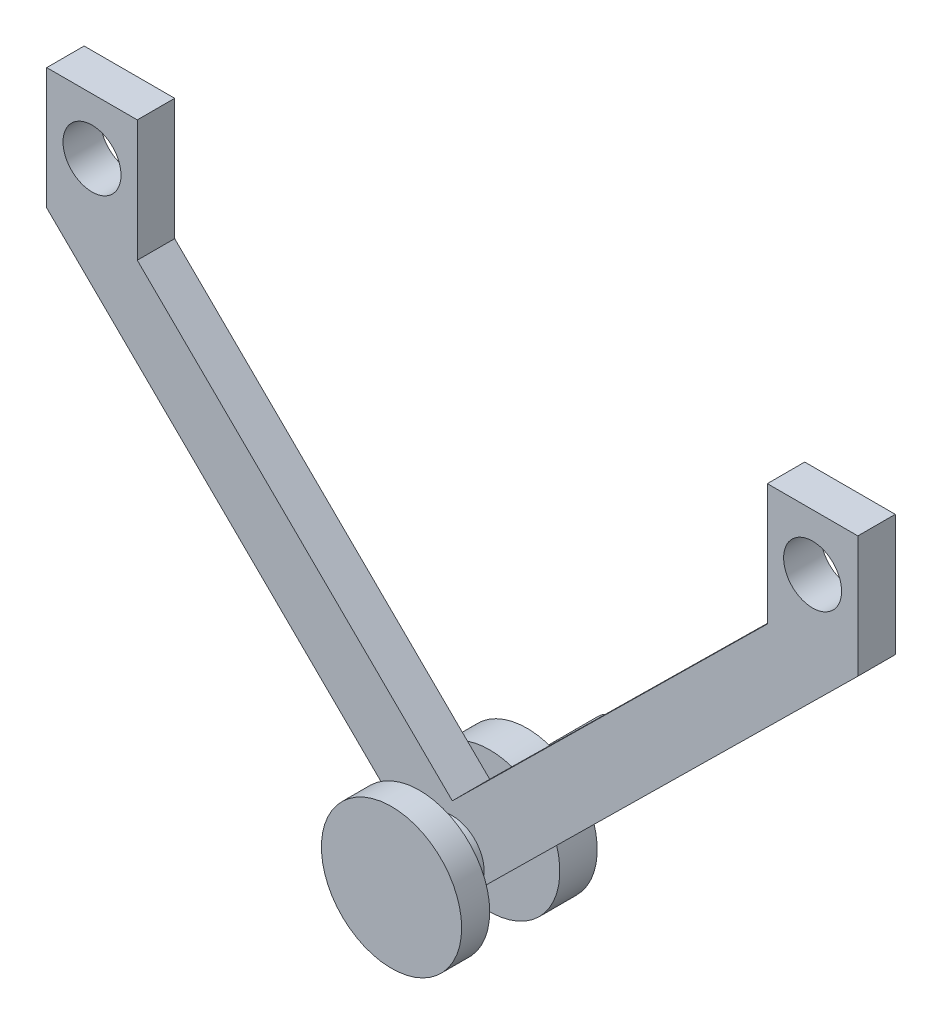
SolidWorks part; units mm, degrees
ref_plane "Спереди" through (0, 0, 0) normal (0, 0, 1) x (1, 0, 0)
ref_plane "Сверху" through (0, 0, 0) normal (0, 1, 0) x (1, 0, 0)
ref_plane "Справа" through (0, 0, 0) normal (1, 0, 0) x (0, 0, -1)
sketch "Эскиз1" plane through (0, 0, 0) normal (0, 0, 1) x (1, 0, 0)
  circle A0 centre (0, 0) radius 7.5
  point P2 (0, 0)
  dimension "D1" = 15
extrude "Бобышка-Вытянуть1" add sketch "Эскиз1" against normal blind 3
sketch "Эскиз2" plane through (0, 0, -3) normal (0, 0, -1) x (-1, 0, 0)
  circle A0 centre (0, 0) radius 3.4
  dimension "D1" = 6.8
extrude "Бобышка-Вытянуть2" add sketch "Эскиз2" along normal blind 11.5
sketch "Эскиз3" plane through (0, 0, -14.5) normal (0, 0, -1) x (-1, 0, 0)
  circle A0 centre (0, 0) radius 7.5
extrude "Бобышка-Вытянуть3" add sketch "Эскиз3" against normal blind 4
sketch "Эскиз4" plane through (0, 0, -14.5) normal (0, 0, -1) x (-1, 0, 0)
  circle A0 centre (0, 0) radius 3.4
  dimension "D1" = 6.8
extrude "Бобышка-Вытянуть4" add sketch "Эскиз4" along normal blind 10
sketch "Эскиз6" plane through (0, 0, -10.5) normal (0, 0, 1) x (1, 0, 0)
  line L0 (0, 86.7657) -> (0, 41.2343) construction
  line L1 (-33.6907, 51) -> (-33.6907, 38)
  line L2 (-3.873, 51) -> (-33.6907, 51) construction
  line L3 (0, 4.7752) -> (-33.6907, 38)
  line L4 (-2.3874, -2.4208) -> (-43.375, 38)
  line L5 (-43.375, 38) -> (-43.375, 51)
  line L6 (-43.375, 51) -> (-33.6907, 51)
  line L7 (0, 4.7752) -> (0, 36) construction
  line L8 (0, 4.7752) -> (33.6907, 38)
  line L9 (2.3874, -2.4208) -> (43.375, 38)
  line L10 (33.6907, 51) -> (33.6907, 38)
  line L11 (43.375, 51) -> (33.6907, 51)
  line L12 (43.375, 38) -> (43.375, 51)
  arc A0 (-2.3874, -2.4208) -> (2.3874, -2.4208) centre (0, 0) ccw
  point P1 (0, 0)
  dimension "D1" = 6.8
  dimension "D2" = 33.6907
  dimension "D3" = 13
  dimension "D4" = 33.6907
extrude "Бобышка-Вытянуть5" add sketch "Эскиз6" along normal blind 4
sketch "Эскиз7" plane through (0, 0, -10.5) normal (0, 0, -1) x (-1, 0, 0)
  circle A0 centre (-38.5329, 45) radius 3.1
  circle A3 centre (38.5329, 45) radius 3.1
  dimension "D1" = 6.2
  dimension "D2" = 6.2
extrude "Вырез-Вытянуть1" cut sketch "Эскиз7" against normal through all
